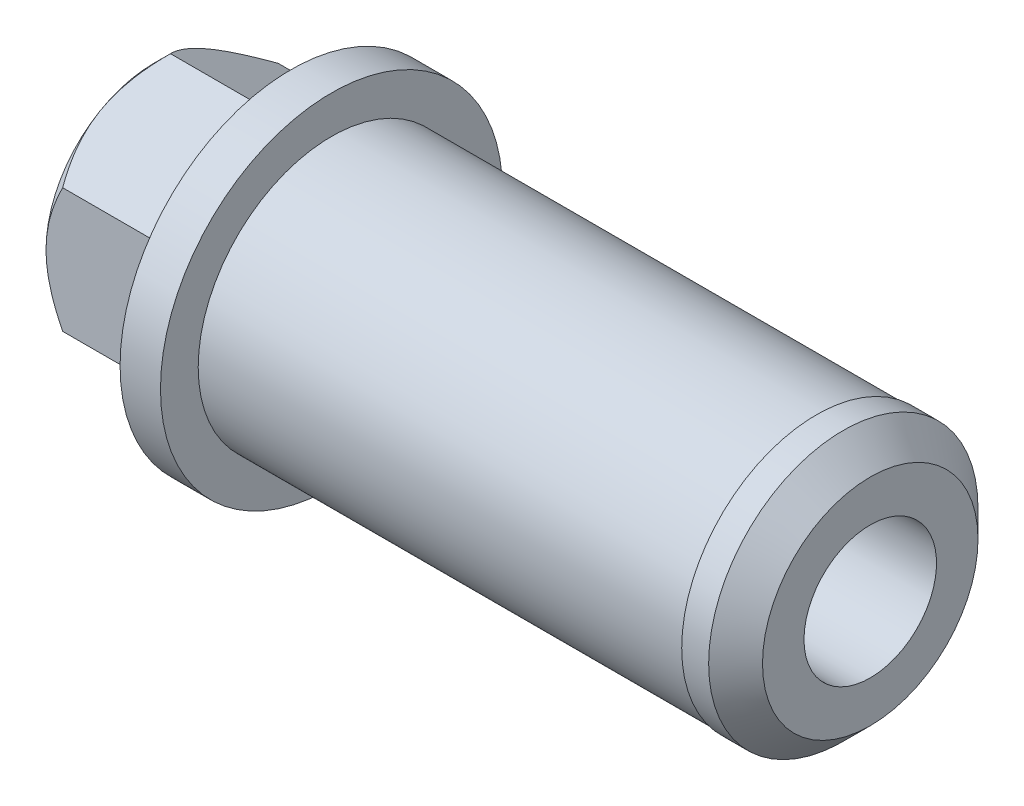
SolidWorks part; units mm, degrees
material "7075-T6 (SN)"
ref_plane "Płaszczyzna XY" through (0, 0, 0) normal (0, 0, 1) x (1, 0, 0)
ref_plane "Płaszczyzna XZ" through (0, 0, 0) normal (0, 1, 0) x (1, 0, 0)
ref_plane "Płaszczyzna YZ" through (0, 0, 0) normal (1, 0, 0) x (0, 0, -1)
sketch "Szkic1" plane through (0, 0, 0) normal (0, 1, 0) x (1, 0, 0)
  line L0 (0, 0) -> (21.5, 0) construction
  line L1 (0, 2.46) -> (0, 6.35)
  line L2 (0, 6.35) -> (1.5, 6.35)
  line L3 (1.5, 6.35) -> (1.5, 4.95)
  line L4 (1.5, 4.95) -> (19.5, 4.95)
  line L5 (19.5, 4.95) -> (19.5, 5)
  line L6 (19.5, 5) -> (21.5, 5)
  line L7 (21.5, 5) -> (21.5, 2.46)
  line L8 (21.5, 2.46) -> (0, 2.46)
  dimension "D1" = 1.5
  dimension "D2" = 10
  dimension "D3" = 9.9
  dimension "D4" = 4.92
  dimension "D5" = 20
  dimension "D6" = 12.7
  dimension "D7" = 2
revolve "Obrót1" add sketch "Szkic1" angle 360 about L0
cosmetic thread "Oznaczenie gwintu1" parameters "D2"=6
chamfer "Sfazowanie1" distance 1 angle 45 1 edges at (21.5, 0, 5)
sketch "Szkic2" plane through (0, 0, 0) normal (-1, 0, 0) x (0, 0, 1)
  line L1 (4, -2.3094) -> (4, 2.3094)
  line L2 (4, 2.3094) -> (0, 4.6188)
  line L3 (0, 4.6188) -> (-4, 2.3094)
  line L4 (-4, 2.3094) -> (-4, -2.3094)
  line L5 (-4, -2.3094) -> (0, -4.6188)
  line L6 (0, -4.6188) -> (4, -2.3094)
  circle A0 centre (0, 0) radius 2.46
  circle A1 centre (0, 0) radius 2.46 construction
  circle A2 centre (0, 0) radius 4 construction
  dimension "D1" = 8
extrude "Dodanie-wyciągnięcie1" add sketch "Szkic2" along normal blind 5.1
sketch "Szkic3" plane through (0, 0, 0) normal (0, 0, 1) x (1, 0, 0)
  line L0 (-5.1, 4.6188) -> (-4.4812, 4.6188)
  line L1 (-5.1, 4.6188) -> (0, 4.6188) construction
  line L2 (-4.4812, 4.6188) -> (-5.1, 4)
  line L3 (-5.1, 4) -> (-5.1, 4.6188)
  line L5 (-4.8366, 0) -> (-6.3219, 0) construction
  dimension "D1" = 45
  dimension "D2" = 8
revolve "Wycięcie-obrót1" cut sketch "Szkic3" angle 360 about L5
chamfer "Sfazowanie2" distance 0.5 angle 45 1 edges at (-5.1, 0, 2.46)
